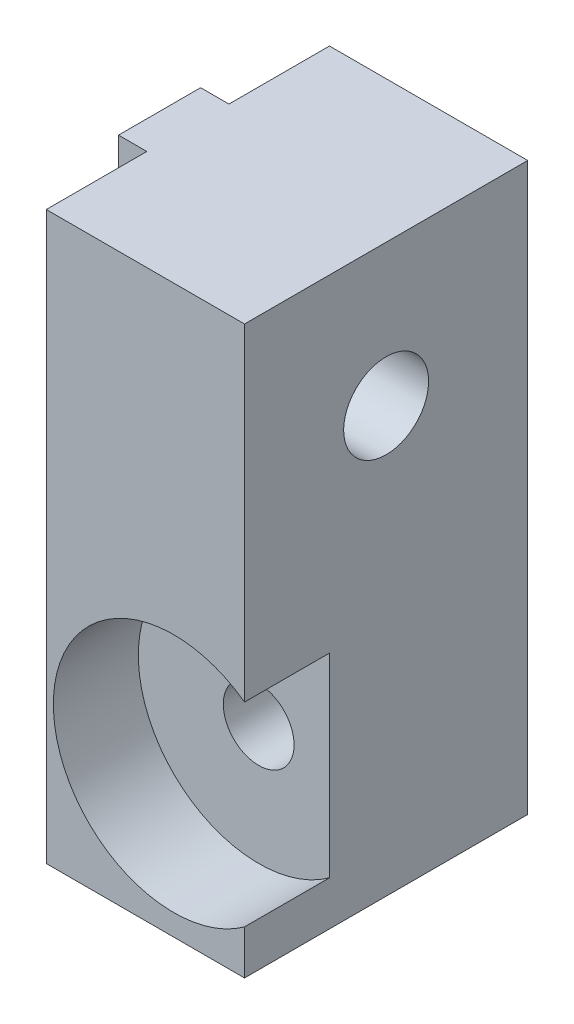
SolidWorks part; units mm, degrees
ref_plane "Front Plane" through (0, 0, 0) normal (0, 0, 1) x (1, 0, 0)
ref_plane "Top Plane" through (0, 0, 0) normal (0, 1, 0) x (1, 0, 0)
ref_plane "Right Plane" through (0, 0, 0) normal (1, 0, 0) x (0, 0, -1)
sketch "Esquisse1" plane through (0, 0, 0) normal (0, 0, 1) x (1, 0, 0)
  line L0 (0, 0) -> (7, 0)
  line L4 (7, 0) -> (7, 20)
  line L5 (7, 20) -> (0, 20)
  line L6 (0, 20) -> (0, 0)
  point P3 (7.321, 0)
  point P4 (7, 0)
  point P5 (7, 0.3684)
  dimension "D2" = 20
  dimension "D3" = 7
extrude "Main" add sketch "Esquisse1" along normal blind 10
sketch "Esquisse4" plane through (0, 0, 0) normal (-1, 0, 0) x (0, 0, 1)
  line L0 (10, 20) -> (0, 20) construction
  line L1 (3.55, 20) -> (6.45, 20)
  line L2 (3.55, 20) -> (3.55, 0)
  line L3 (3.55, 0) -> (6.45, 0)
  line L4 (6.45, 20) -> (6.45, 0)
  line L5 (10, 0) -> (0, 0) construction
  point P8 (5, 20)
  point P9 (5, 20)
  dimension "D1" = 2.9
extrude "MakerBeamFixVertical" add sketch "Esquisse4" along normal blind 1
sketch "Esquisse2" plane through (0, 0, 0) normal (-1, 0, 0) x (0, 0, 1)
  line L0 (10, 20) -> (6.45, 20) construction
  line L1 (10, 20) -> (0, 20) construction
  circle A0 centre (5, 15) radius 1.5
  point P9 (5, 20)
  dimension "D1" = 3
  dimension "D2" = 5
extrude "MakerBeamVerticalHole" cut sketch "Esquisse2" against normal through all both and the other way through all
sketch "Sketch1" plane through (0, 0, 10) normal (0, 0, 1) x (1, 0, 0)
  line L0 (0, 0) -> (7, 0) construction
  line L1 (7, 20) -> (0, 20) construction
  line L2 (0, 0) -> (0, 14.6159) construction
  circle A0 centre (4.5, 5) radius 1.25
  point P4 (3.5, 20)
  point P8 (15.6422, 6.1417)
  dimension "D1" = 2.5
  dimension "D2" = 5
  dimension "D3" = 4.5
extrude "Cut-Extrude1" cut sketch "Sketch1" against normal through all
sketch "Sketch2" plane through (0, 0, 10) normal (0, 0, 1) x (1, 0, 0)
  circle A0 centre (4.5, 5) radius 4.25
  dimension "D1" = 8.5
extrude "Cut-Extrude2" cut sketch "Sketch2" against normal blind 3
